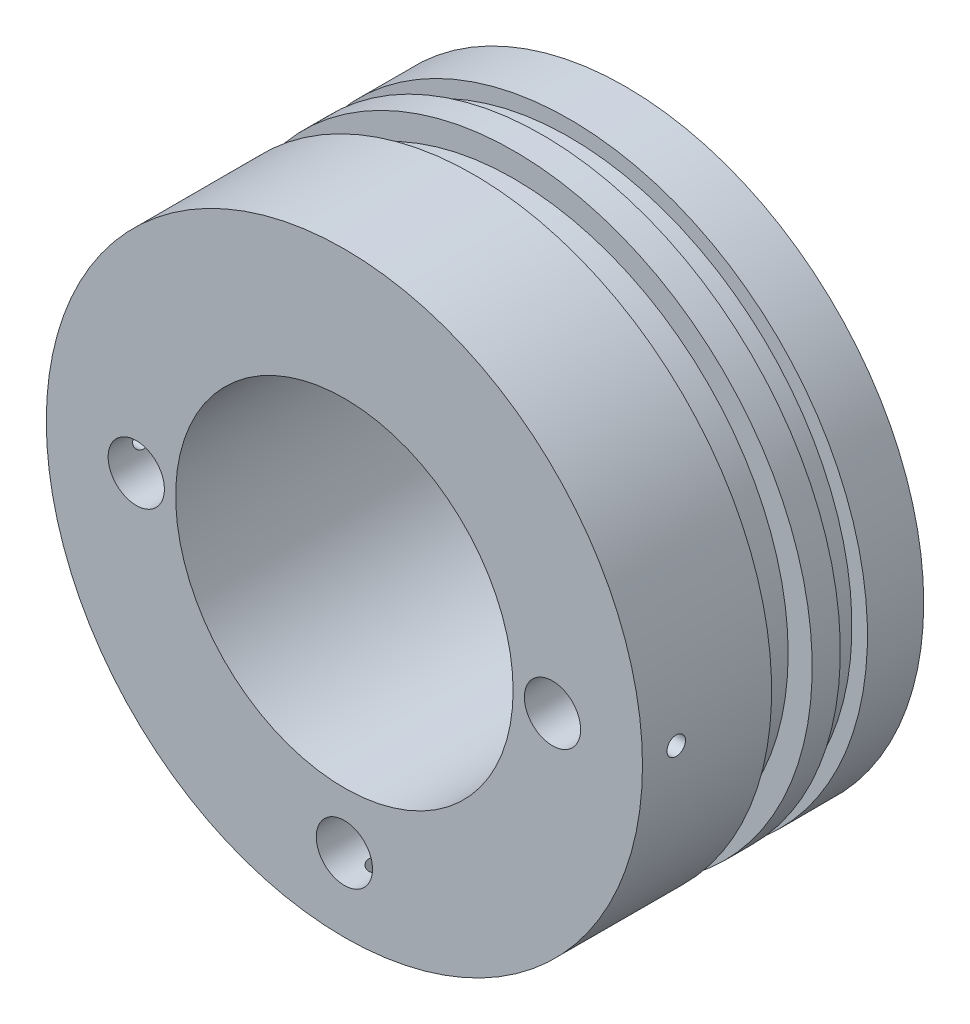
SolidWorks part; units mm, degrees
material "1060 Alloy"
ref_plane "Front Plane" through (0, 0, 0) normal (0, 0, 1) x (1, 0, 0)
ref_plane "Top Plane" through (0, 0, 0) normal (0, 1, 0) x (1, 0, 0)
ref_plane "Right Plane" through (0, 0, 0) normal (1, 0, 0) x (0, 0, -1)
sketch "Sketch1" plane through (0, 0, 0) normal (0, 0, 1) x (1, 0, 0)
  circle A0 centre (0, 0) radius 53
  dimension "D1" = 106
extrude "Boss-Extrude1" add sketch "Sketch1" along normal blind 50
hole_wizard "Ø10.0mm Dowel Hole1" positions "Sketch7" profile "Sketch9" hole size "Ø10.0" standard "ISO"
sketch "Sketch7" plane through (0, 0, 50) normal (0, 0, 1) x (1, 0, 0)
  point P0 (-37, 0)
  point P2 (37, 0)
  point P4 (0, -40)
  dimension "D1" = 37
  dimension "D2" = 37
  dimension "D3" = 40
sketch "Sketch9" plane through (-37, 0, 50) normal (1, 0, 0) x (0, -1, 0)
  line L0 (0, 0) -> (0, 20.5043)
  line L1 (0, 20.5043) -> (5, 17.5)
  line L2 (5, 17.5) -> (5, 0)
  line L5 (5, 0) -> (0, 0)
  line L10 (0, 20.5043) -> (-5, 17.5) construction
  line L11 (0, -6.35) -> (0, 107.95) construction
  dimension "Hole Dia." = 10
  dimension "Hole Depth" = 17.5
  dimension "Drill Angle" = 118
ref_plane "Plane1" through (-53, 0, 0) normal (-1, 0, 0) x (0, 0, 1)
hole_wizard "M4 Tapped Hole1" positions "Sketch4" profile "Sketch5" tap size "M4" standard "ISO"
sketch "Sketch4" plane through (-53, 0, 0) normal (-1, 0, 0) x (0, 0, 1)
  line L0 (50, -53) -> (50, 53) construction
  point P0 (44, 0)
  dimension "D1" = 6
sketch "Sketch5" plane through (-53, 0, 44) normal (0, 1, 0) x (0, 0, 1)
  line L0 (0, 0) -> (0, 85)
  line L1 (0, 85) -> (1.65, 85)
  line L2 (1.65, 85) -> (1.65, 0)
  line L5 (1.65, 0) -> (0, 0)
  line L11 (0, -6.35) -> (0, 107.95) construction
  dimension "Thru Tap Drill Dia." = 3.3
  dimension "Thru Tap Drill Depth" = 85
cosmetic thread "Hole Thread1" parameters "D2"=4
pattern_circular "CirPattern1" count 3 every 90 about axis through (0, 0, 50) along (0, 0, 1) of "M4 Tapped Hole1"
sketch "Sketch11" plane through (0, 0, 50) normal (0, 0, 1) x (1, 0, 0)
  circle A0 centre (0, 0) radius 30
  dimension "D1" = 60
extrude "Cut-Extrude2" cut sketch "Sketch11" against normal blind 45
sketch "Sketch12" plane through (0, 0, 0) normal (1, 0, 0) x (0, 0, -1)
  line L0 (0, 53) -> (-50, 53) construction
  line L1 (-10, 53) -> (-14.826, 53)
  line L2 (-10, 53) -> (-10, 50.2348)
  line L3 (-10, 50.2348) -> (-14.826, 50.2348)
  line L4 (-14.826, 53) -> (-14.826, 50.2348)
  line L5 (0, -53) -> (0, 53) construction
  line L6 (0, 0) -> (-18.8162, 0) construction
  line L8 (-19.826, 53) -> (-27.0396, 53)
  line L9 (-19.826, 53) -> (-19.826, 48.7274)
  line L10 (-19.826, 48.7274) -> (-27.0396, 48.7274)
  line L11 (-27.0396, 53) -> (-27.0396, 48.7274)
  point P14 (-19.826, 50.8637)
  dimension "D1" = 10
  dimension "D2" = 4.826
  dimension "D3" = 50.2348
  dimension "D4" = 7.2136
  dimension "D5" = 5
  dimension "D6" = 48.7274
revolve "Cut-Revolve1" cut sketch "Sketch12" angle 360 about L6
sketch "Sketch14" plane through (0, 0, 0) normal (1, 0, 0) x (0, 0, -1)
  line L0 (0, -53) -> (0, 53) construction
  line L1 (0, 27.1526) -> (-2.667, 27.1526)
  line L2 (0, 27.1526) -> (0, 22.5806)
  line L3 (0, 22.5806) -> (-2.667, 22.5806)
  line L4 (-2.667, 27.1526) -> (-2.667, 22.5806)
  line L6 (0, 0) -> (21.0083, 0) construction
  dimension "D1" = 2.667
  dimension "D2" = 4.572
  dimension "D3" = 22.5806
revolve "Cut-Revolve2" cut sketch "Sketch14" angle 360 about L6
sketch "Sketch15" plane through (0, 0, 0) normal (0, 0, -1) x (-1, 0, 0)
  line L0 (0, 0) -> (15.7797, 0) construction
  line L1 (0, 0) -> (-10.6066, 10.6066) construction
  line L2 (0, 0) -> (0, -15) construction
  line L3 (0, 0) -> (10.6066, 10.6066) construction
  circle A0 centre (-10.6066, 10.6066) radius 4.5
  circle A1 centre (0, -15) radius 4.5
  circle A2 centre (10.6066, 10.6066) radius 4.5
  dimension "D1" = 45
  dimension "D6" = 9
  dimension "D7" = 9
  dimension "D8" = 9
  dimension "D2" = 90
  dimension "D3" = 15
  dimension "D4" = 15
  dimension "D5" = 15
extrude "Cut-Extrude3" cut sketch "Sketch15" against normal blind 10
hole_wizard "M5 Tapped Hole1" positions "Sketch16" profile "Sketch17" tap size "M5" standard "ISO"
sketch "Sketch16" plane through (0, 0, 0) normal (0, 0, -1) x (-1, 0, 0)
  line L0 (0, 0) -> (28.2843, 28.2843) construction
  line L3 (0, 0) -> (0, 39.1182) construction
  point P0 (28.2843, 28.2843)
  dimension "D1" = 45
  dimension "D2" = 40
sketch "Sketch17" plane through (-28.2843, 28.2843, 0) normal (1, 0, 0) x (0, 1, 0)
  line L0 (0, 0) -> (0, 15.2618)
  line L1 (0, 15.2618) -> (2.1, 14)
  line L2 (2.1, 14) -> (2.1, 0)
  line L5 (2.1, 0) -> (0, 0)
  line L10 (0, 15.2618) -> (-2.1, 14) construction
  line L11 (0, -6.35) -> (0, 107.95) construction
  dimension "Tap Drill Dia." = 4.2
  dimension "Tap Drill Depth" = 14
  dimension "Drill Angle" = 118
cosmetic thread "Hole Thread5" parameters "D1"=10, "D2"=5
pattern_circular "CirPattern2" count 4 over 360 about axis through (0, 0, 0) along (0, 0, 1) of "M5 Tapped Hole1"
equation "\"3.995هى\"=42.5"
